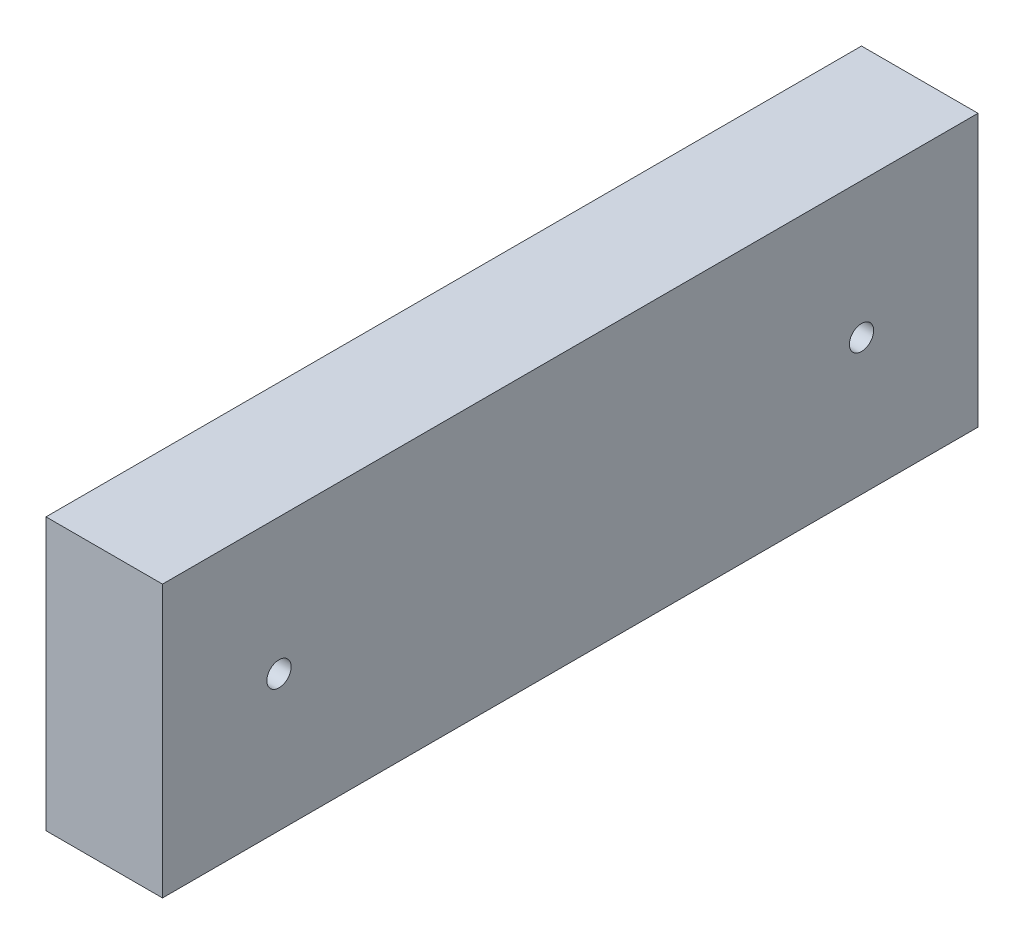
SolidWorks part; units mm, degrees
material "Pine"
ref_plane "Front Plane" through (0, 0, 0) normal (0, 0, 1) x (1, 0, 0)
ref_plane "Top Plane" through (0, 0, 0) normal (0, 1, 0) x (1, 0, 0)
ref_plane "Right Plane" through (0, 0, 0) normal (1, 0, 0) x (0, 0, -1)
sketch "Sketch1" plane through (0, 0, 0) normal (0, 0, 1) x (1, 0, 0)
  line L1 (-19.05, -44.45) -> (19.05, -44.45)
  line L2 (-19.05, -44.45) -> (-19.05, 44.45)
  line L3 (-19.05, 44.45) -> (19.05, 44.45)
  line L4 (19.05, -44.45) -> (19.05, 44.45)
  line L5 (-19.05, -44.45) -> (19.05, 44.45) construction
  line L6 (-19.05, 44.45) -> (19.05, -44.45) construction
  point P0 (0, 0)
  dimension "D1" = 88.9
  dimension "D2" = 38.1
extrude "Boss-Extrude1" add sketch "Sketch1" along normal blind 266.7
sketch "Sketch2" plane through (19.05, 0, 0) normal (1, 0, 0) x (0, 0, -1)
  line L0 (-266.7, -44.45) -> (-266.7, 44.45) construction
  line L1 (0, -44.45) -> (0, 44.45) construction
  point P0 (-38.1, 0)
  point P1 (-228.6, 0)
  dimension "D1" = 38.1
  dimension "D2" = 38.1
hole_wizard "5/16 (0.3125) Diameter Hole1" positions "Sketch3" profile "Sketch4" hole size "5/16" standard "ANSI Inch" end condition through all
sketch "Sketch3" plane through (19.05, 0, 0) normal (1, 0, 0) x (0, 0, -1)
  point P0 (-228.6, 0)
  point P3 (-38.1, 0)
sketch "Sketch4" plane through (19.05, 0, 228.6) normal (0, 1, 0) x (0, 0, -1)
  line L0 (0, 0) -> (0, 38.1)
  line L1 (0, 38.1) -> (3.9687, 38.1)
  line L2 (3.9687, 38.1) -> (3.9687, 0)
  line L5 (3.9687, 0) -> (0, 0)
  line L11 (0, -6.35) -> (0, 107.95) construction
  dimension "Thru Hole Dia." = 7.9375
  dimension "Thru Hole Depth" = 38.1
